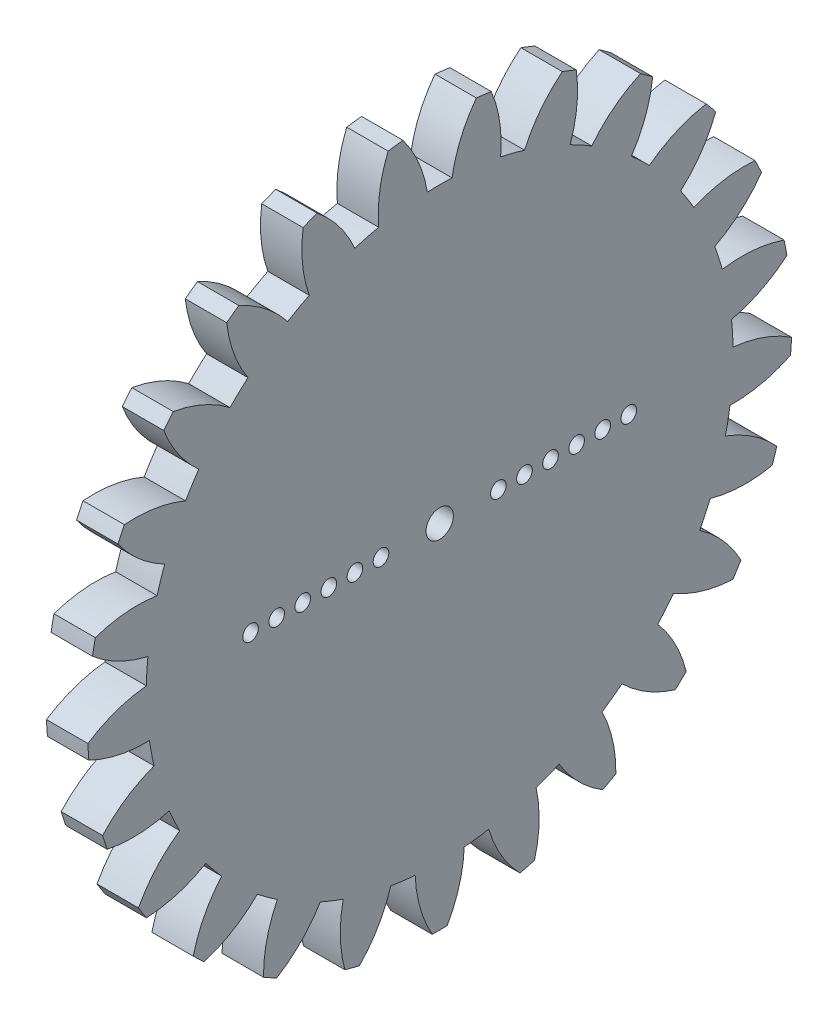
SolidWorks part; units mm, degrees
ref_plane "Plane1" through (0, 0, 0) normal (0, 0, 1) x (1, 0, 0)
ref_plane "Plane2" through (0, 0, 0) normal (0, 1, 0) x (1, 0, 0)
ref_plane "Plane3" through (0, 0, 0) normal (1, 0, 0) x (0, 0, -1)
sketch "HoldingSke" plane through (0, 0, 0) normal (0, 1, 0) x (1, 0, 0)
  line L0 (0, 0) -> (0.4532, -0.2113)
  line L1 (-15, 0) -> (100, 0) construction
  line L2 (0, 0) -> (-2.1039, 2.3779)
  line L3 (0, 0) -> (-11.863, 4.5341)
  line L4 (0, 0) -> (7.8269, 3.6497)
  line L5 (0, 0) -> (-46.8476, -17.4728)
  line L6 (0, 0) -> (-8.2896, -5.593)
  line L7 (-2.1039, 2.3779) -> (8.6586, 51.2059)
  line L8 (-76.2, 54.61) -> (-74.4, 54.61)
  line L9 (-71.009, 38.7566) -> (-53.1078, 45.2721)
  line L10 (-76.2, 71.12) -> (104.1128, 71.12)
  line L11 (0, 0) -> (-10, 0)
  line L12 (-76.2, 101.6) -> (-76.133, 101.6)
  line L13 (24.9733, 27.94) -> (52.9518, 28.4284)
  line L14 (24.9733, 27.94) -> (24.9743, 27.94)
  line L15 (24.9733, 27.94) -> (100.4006, 29.5858)
  line L16 (-63.627, -2) -> (-12.827, -2)
  circle A0 centre (0, 0) radius 5
  circle A1 centre (0, 0) radius 22.499
  circle A2 centre (0, 0) radius 37.5
  circle A3 centre (0, 0) radius 5
  dimension "MHD" = 44.998
  dimension "Hub_dia" = 75
  dimension "Bore" = 10
  dimension "MBD" = 10
  dimension "Num_teeth" = 25
  dimension "Pitch" = 0.5
  dimension "Overall_len" = 50
  dimension "Show_teeth" = 25
  dimension "Thickness" = 10
  dimension "OAL" = 50.0001
  dimension "T_dim" = 1.8
  dimension "Ap" = 20
  dimension "H" = 19.05
  dimension "Pitch_radius" = 180.3128
  dimension "Width" = 10
  dimension "Backlash" = 0.067
  dimension "Addendum_fac" = 1
  dimension "Dedendum_fac" = 1.25
  dimension "Clearance_fac" = 0.25
  dimension "Dedendum_add" = 0.001
  dimension "Module" = 2
sketch "BasProSke" plane through (0, 0, 0) normal (0, 1, 0) x (1, 0, 0)
  line L0 (-10, 0) -> (60, 0) construction
  line L1 (0, 0) -> (0, 27)
  line L2 (0, 0) -> (10, 0)
  line L3 (10, 0) -> (10, 27)
  line L4 (10, 27) -> (0, 27)
  dimension "Thickness" = 10
  dimension "Diameter" = 54
revolve "Base-Revolve" add sketch "BasProSke" angle 360 about L0
sketch "TooCutSke" plane through (0, 0, 0) normal (1, 0, 0) x (0, 0, -1)
  line L1 (0, 0) -> (0, 107) construction
  line L2 (0, 0) -> (-1.687, 24.943) construction
  line L3 (0, 0) -> (-6.2561, 49.5219) construction
  line L4 (-1.687, 24.943) -> (-3.128, 24.761) construction
  arc A0 (0.9462, 22.4791) -> (-0.9462, 22.4791) centre (0, 0) ccw
  arc A1 (2.8295, 26.8769) -> (-2.8295, 26.8769) centre (0, 0) ccw
  circle A2 centre (0, 0) radius 25 construction
  circle A3 centre (0, 0) radius 23.4923 construction
  arc A4 (-0.9462, 22.4791) -> (-2.8295, 26.8769) centre (-10.8135, 20.8556) ccw
  arc A5 (2.8295, 26.8769) -> (0.9462, 22.4791) centre (10.8135, 20.8556) ccw
  dimension "Root_dia" = 44.998
  dimension "Overcut_dia" = 54.0508
  dimension "Pitch_dia" = 50
  dimension "Base_dia" = 46.9846
  dimension "Flank_rad" = 10
  dimension "Half_ang" = 7.2
  dimension "Half_CT" = 1.4525
extrude "ToothCut" cut sketch "TooCutSke" along normal through all
fillet "Breaks" [suppressed] radius 0.04
fillet "RootFillets" [suppressed] radius 0.501
pattern_circular "TeethCuts" count 25 over 360 about axis through (0, 0, 0) along (1, 0, 0) of "ToothCut", "RootFillets", "Breaks"
sketch "HubNeaOneSke" plane through (0, 0, 0) normal (-1, 0, 0) x (0, 0, 1)
  circle A0 centre (0, 0) radius 22.499
  dimension "Diameter" = 44.998
extrude "HubNearOne" [suppressed] add sketch "HubNeaOneSke" along normal blind 40.0001
sketch "HubNeaBotSke" plane through (0, 0, 0) normal (-1, 0, 0) x (0, 0, 1)
  circle A0 centre (0, 0) radius 22.499
  dimension "Diameter" = 44.998
extrude "HubNearBoth" [suppressed] add sketch "HubNeaBotSke" along normal blind 20
ref_plane "FarPln" through (10, 0, 0) normal (1, 0, 0) x (0, 0, -1)
sketch "HubFarSke" plane through (10, 0, 0) normal (1, 0, 0) x (0, 0, -1)
  circle A0 centre (0, 0) radius 22.499
  dimension "Diameter" = 44.998
extrude "HubFar" [suppressed] add sketch "HubFarSke" along normal blind 20
sketch "BorSke" plane through (0, 0, 0) normal (1, 0, 0) x (0, 0, -1)
  circle A0 centre (0, 0) radius 5
  dimension "Diameter" = 10
extrude "Bore" [suppressed] cut sketch "BorSke" along normal mid plane 100.0001
sketch "KeySke" plane through (0, 0, 0) normal (1, 0, 0) x (0, 0, -1)
  line L0 (-2, 0) -> (-2, 6.8)
  line L1 (-2, 6.8) -> (2, 6.8)
  line L2 (2, 6.8) -> (2, 0)
  line L3 (0, 0) -> (0, 34) construction
  line L4 (-2, 0) -> (2, 0)
  dimension "Offset" = 6.8
  dimension "Width" = 4
extrude "Keyway" [suppressed] cut sketch "KeySke" along normal mid plane 100.0001
pattern_circular "Keyway2" [suppressed] count 2 every 90 about axis through (-10, 0, 0) along (1, 0, 0)
sketch "Sketch1" plane through (10, 0, 0) normal (1, 0, 0) x (0, 0, -1)
  arc A100 (-26.6237, 4.4923) -> (-22.3753, 2.3558) centre (-20.1355, 12.1017) ccw
  arc A101 (-26.6237, 4.4923) -> (-22.3753, 2.3558) centre (-20.1355, 12.1017) ccw
  arc A102 (-22.3753, 2.3558) -> (-22.4941, 0.4672) centre (0, 0) ccw
  arc A103 (-26.9768, -1.12) -> (-26.9044, -2.2699) centre (0, 0) ccw
  arc A104 (-22.3753, 2.3558) -> (-22.4941, 0.4672) centre (0, 0) ccw
  arc A105 (-22.4941, 0.4672) -> (-26.9768, -1.12) centre (-21.4935, -9.4826) ccw
  arc A106 (-22.4941, 0.4672) -> (-26.9768, -1.12) centre (-21.4935, -9.4826) ccw
  arc A107 (-26.9044, -2.2699) -> (-22.2582, -3.2828) centre (-22.5125, 6.714) ccw
  arc A108 (-26.9044, -2.2699) -> (-22.2582, -3.2828) centre (-22.5125, 6.714) ccw
  arc A109 (-22.2582, -3.2828) -> (-21.9036, -5.1416) centre (0, 0) ccw
  arc A110 (-22.2582, -3.2828) -> (-21.9036, -5.1416) centre (0, 0) ccw
  arc A111 (-21.9036, -5.1416) -> (-25.8507, -7.7937) centre (-18.46, -14.5299) ccw
  arc A112 (-21.9036, -5.1416) -> (-25.8507, -7.7937) centre (-18.46, -14.5299) ccw
  arc A113 (-25.8507, -7.7937) -> (-25.4947, -8.8895) centre (0, 0) ccw
  arc A114 (-25.8507, -7.7937) -> (-25.4947, -8.8895) centre (0, 0) ccw
  arc A115 (-25.4947, -8.8895) -> (-20.7425, -8.715) centre (-23.4749, 0.9044) ccw
  arc A116 (-25.4947, -8.8895) -> (-20.7425, -8.715) centre (-23.4749, 0.9044) ccw
  arc A117 (-20.7425, -8.715) -> (-19.9368, -10.4272) centre (0, 0) ccw
  arc A118 (-20.7425, -8.715) -> (-19.9368, -10.4272) centre (0, 0) ccw
  arc A119 (-19.9368, -10.4272) -> (-23.1004, -13.9776) centre (-14.2666, -18.6642) ccw
  arc A120 (-19.9368, -10.4272) -> (-23.1004, -13.9776) centre (-14.2666, -18.6642) ccw
  arc A121 (-23.1004, -13.9776) -> (-22.483, -14.9504) centre (0, 0) ccw
  arc A122 (-23.1004, -13.9776) -> (-22.483, -14.9504) centre (0, 0) ccw
  arc A123 (-22.483, -14.9504) -> (-17.9235, -13.5997) centre (-22.9623, -4.9619) ccw
  arc A124 (-22.483, -14.9504) -> (-17.9235, -13.5997) centre (-22.9623, -4.9619) ccw
  arc A125 (-17.9235, -13.5997) -> (-16.7173, -15.0577) centre (0, 0) ccw
  arc A126 (-17.9235, -13.5997) -> (-16.7173, -15.0577) centre (0, 0) ccw
  arc A127 (-16.7173, -15.0577) -> (-18.8985, -19.2833) centre (-9.1768, -21.6258) ccw
  arc A128 (-16.7173, -15.0577) -> (-18.8985, -19.2833) centre (-9.1768, -21.6258) ccw
  arc A129 (-18.8985, -19.2833) -> (-18.0586, -20.072) centre (0, 0) ccw
  arc A130 (-18.8985, -19.2833) -> (-18.0586, -20.072) centre (0, 0) ccw
  arc A131 (-18.0586, -20.072) -> (-13.9783, -17.6298) centre (-21.0069, -10.5165) ccw
  arc A132 (-18.0586, -20.072) -> (-13.9783, -17.6298) centre (-21.0069, -10.5165) ccw
  arc A133 (-13.9783, -17.6298) -> (-12.4474, -18.7421) centre (0, 0) ccw
  arc A134 (-13.9783, -17.6298) -> (-12.4474, -18.7421) centre (0, 0) ccw
  arc A135 (-12.4474, -18.7421) -> (-13.5092, -23.3774) centre (-3.5103, -23.2286) ccw
  arc A136 (-12.4474, -18.7421) -> (-13.5092, -23.3774) centre (-3.5103, -23.2286) ccw
  arc A137 (-13.5092, -23.3774) -> (-12.4996, -23.9324) centre (0, 0) ccw
  arc A138 (-13.5092, -23.3774) -> (-12.4996, -23.9324) centre (0, 0) ccw
  arc A139 (-12.4996, -23.9324) -> (-9.1548, -20.5522) centre (-17.7316, -15.4104) ccw
  arc A140 (-12.4996, -23.9324) -> (-9.1548, -20.5522) centre (-17.7316, -15.4104) ccw
  arc A141 (-9.1548, -20.5522) -> (-7.3954, -21.2488) centre (0, 0) ccw
  arc A142 (-9.1548, -20.5522) -> (-7.3954, -21.2488) centre (0, 0) ccw
  arc A143 (-7.3954, -21.2488) -> (-7.2711, -26.0025) centre (2.3767, -23.3718) ccw
  arc A144 (-7.3954, -21.2488) -> (-7.2711, -26.0025) centre (2.3767, -23.3718) ccw
  arc A145 (-7.2711, -26.0025) -> (-6.1551, -26.2891) centre (0, 0) ccw
  arc A146 (-7.2711, -26.0025) -> (-6.1551, -26.2891) centre (0, 0) ccw
  arc A147 (-6.1551, -26.2891) -> (-3.7561, -22.1833) centre (-13.3421, -19.3359) ccw
  arc A148 (-6.1551, -26.2891) -> (-3.7561, -22.1833) centre (-13.3421, -19.3359) ccw
  arc A149 (-3.7561, -22.1833) -> (-1.8787, -22.4204) centre (0, 0) ccw
  arc A150 (-3.7561, -22.1833) -> (-1.8787, -22.4204) centre (0, 0) ccw
  arc A151 (-1.8787, -22.4204) -> (-0.5761, -26.9939) centre (8.1143, -22.0465) ccw
  arc A152 (-1.8787, -22.4204) -> (-0.5761, -26.9939) centre (8.1143, -22.0465) ccw
  arc A153 (-0.5761, -26.9939) -> (0.5761, -26.9939) centre (0, 0) ccw
  arc A154 (-0.5761, -26.9939) -> (0.5761, -26.9939) centre (0, 0) ccw
  arc A155 (0.5761, -26.9939) -> (1.8787, -22.4204) centre (-8.1143, -22.0465) ccw
  arc A156 (0.5761, -26.9939) -> (1.8787, -22.4204) centre (-8.1143, -22.0465) ccw
  arc A157 (1.8787, -22.4204) -> (3.7561, -22.1833) centre (0, 0) ccw
  arc A158 (1.8787, -22.4204) -> (3.7561, -22.1833) centre (0, 0) ccw
  arc A159 (3.7561, -22.1833) -> (6.1551, -26.2891) centre (13.3421, -19.3359) ccw
  arc A160 (3.7561, -22.1833) -> (6.1551, -26.2891) centre (13.3421, -19.3359) ccw
  arc A161 (6.1551, -26.2891) -> (7.2711, -26.0025) centre (0, 0) ccw
  arc A162 (6.1551, -26.2891) -> (7.2711, -26.0025) centre (0, 0) ccw
  arc A163 (7.2711, -26.0025) -> (7.3954, -21.2488) centre (-2.3767, -23.3718) ccw
  arc A164 (7.2711, -26.0025) -> (7.3954, -21.2488) centre (-2.3767, -23.3718) ccw
  arc A165 (7.3954, -21.2488) -> (9.1548, -20.5522) centre (0, 0) ccw
  arc A166 (7.3954, -21.2488) -> (9.1548, -20.5522) centre (0, 0) ccw
  arc A167 (9.1548, -20.5522) -> (12.4996, -23.9324) centre (17.7316, -15.4104) ccw
  arc A168 (9.1548, -20.5522) -> (12.4996, -23.9324) centre (17.7316, -15.4104) ccw
  arc A169 (12.4996, -23.9324) -> (13.5092, -23.3774) centre (0, 0) ccw
  arc A170 (12.4996, -23.9324) -> (13.5092, -23.3774) centre (0, 0) ccw
  arc A171 (13.5092, -23.3774) -> (12.4474, -18.7421) centre (3.5103, -23.2286) ccw
  arc A172 (13.5092, -23.3774) -> (12.4474, -18.7421) centre (3.5103, -23.2286) ccw
  arc A173 (12.4474, -18.7421) -> (13.9783, -17.6298) centre (0, 0) ccw
  arc A174 (12.4474, -18.7421) -> (13.9783, -17.6298) centre (0, 0) ccw
  arc A175 (13.9783, -17.6298) -> (18.0586, -20.072) centre (21.0069, -10.5165) ccw
  arc A176 (2.8117, 26.8532) -> (0.9462, 22.4791) centre (10.8135, 20.8556) ccw
  arc A177 (0.9462, 22.4791) -> (-0.9462, 22.4791) centre (0, 0) ccw
  arc A178 (-0.9462, 22.4791) -> (-2.8117, 26.8532) centre (-10.8135, 20.8556) ccw
  arc A179 (13.9783, -17.6298) -> (18.0586, -20.072) centre (21.0069, -10.5165) ccw
  arc A180 (18.0586, -20.072) -> (18.8985, -19.2833) centre (0, 0) ccw
  arc A181 (18.0586, -20.072) -> (18.8985, -19.2833) centre (0, 0) ccw
  arc A182 (18.8985, -19.2833) -> (16.7173, -15.0577) centre (9.1768, -21.6258) ccw
  arc A183 (18.8985, -19.2833) -> (16.7173, -15.0577) centre (9.1768, -21.6258) ccw
  arc A184 (16.7173, -15.0577) -> (17.9235, -13.5997) centre (0, 0) ccw
  arc A185 (16.7173, -15.0577) -> (17.9235, -13.5997) centre (0, 0) ccw
  arc A186 (17.9235, -13.5997) -> (22.483, -14.9504) centre (22.9623, -4.9619) ccw
  arc A187 (17.9235, -13.5997) -> (22.483, -14.9504) centre (22.9623, -4.9619) ccw
  arc A188 (22.483, -14.9504) -> (23.1004, -13.9776) centre (0, 0) ccw
  arc A189 (22.483, -14.9504) -> (23.1004, -13.9776) centre (0, 0) ccw
  arc A190 (23.1004, -13.9776) -> (19.9368, -10.4272) centre (14.2666, -18.6642) ccw
  arc A191 (23.1004, -13.9776) -> (19.9368, -10.4272) centre (14.2666, -18.6642) ccw
  arc A192 (19.9368, -10.4272) -> (20.7425, -8.715) centre (0, 0) ccw
  arc A193 (19.9368, -10.4272) -> (20.7425, -8.715) centre (0, 0) ccw
  arc A194 (20.7425, -8.715) -> (25.4947, -8.8895) centre (23.4749, 0.9044) ccw
  arc A195 (20.7425, -8.715) -> (25.4947, -8.8895) centre (23.4749, 0.9044) ccw
  arc A196 (25.4947, -8.8895) -> (25.8507, -7.7937) centre (0, 0) ccw
  arc A197 (25.4947, -8.8895) -> (25.8507, -7.7937) centre (0, 0) ccw
  arc A198 (25.8507, -7.7937) -> (21.9036, -5.1416) centre (18.46, -14.5299) ccw
  arc A199 (25.8507, -7.7937) -> (21.9036, -5.1416) centre (18.46, -14.5299) ccw
  arc A203 (-26.9768, -1.12) -> (-26.9044, -2.2699) centre (0, 0) ccw
  arc A276 (2.8117, 26.8532) -> (0.9462, 22.4791) centre (10.8135, 20.8556) ccw
  arc A277 (0.9462, 22.4791) -> (-0.9462, 22.4791) centre (0, 0) ccw
  arc A278 (-0.9462, 22.4791) -> (-2.8117, 26.8532) centre (-10.8135, 20.8556) ccw
  arc A300 (21.9036, -5.1416) -> (22.2582, -3.2828) centre (0, 0) ccw
  arc A301 (21.9036, -5.1416) -> (22.2582, -3.2828) centre (0, 0) ccw
  arc A302 (22.2582, -3.2828) -> (26.9044, -2.2699) centre (22.5125, 6.714) ccw
  arc A303 (22.2582, -3.2828) -> (26.9044, -2.2699) centre (22.5125, 6.714) ccw
  arc A304 (26.9044, -2.2699) -> (26.9768, -1.12) centre (0, 0) ccw
  arc A305 (26.9044, -2.2699) -> (26.9768, -1.12) centre (0, 0) ccw
  arc A306 (26.9768, -1.12) -> (22.4941, 0.4672) centre (21.4935, -9.4826) ccw
  arc A307 (26.9768, -1.12) -> (22.4941, 0.4672) centre (21.4935, -9.4826) ccw
  arc A308 (22.4941, 0.4672) -> (22.3753, 2.3558) centre (0, 0) ccw
  arc A309 (22.4941, 0.4672) -> (22.3753, 2.3558) centre (0, 0) ccw
  arc A310 (22.3753, 2.3558) -> (26.6237, 4.4923) centre (20.1355, 12.1017) ccw
  arc A311 (22.3753, 2.3558) -> (26.6237, 4.4923) centre (20.1355, 12.1017) ccw
  arc A312 (26.6237, 4.4923) -> (26.4078, 5.624) centre (0, 0) ccw
  arc A313 (26.6237, 4.4923) -> (26.4078, 5.624) centre (0, 0) ccw
  arc A314 (26.4078, 5.624) -> (21.6713, 6.0466) centre (23.1764, -3.8395) ccw
  arc A315 (26.4078, 5.624) -> (21.6713, 6.0466) centre (23.1764, -3.8395) ccw
  arc A316 (21.6713, 6.0466) -> (21.0865, 7.8463) centre (0, 0) ccw
  arc A317 (21.6713, 6.0466) -> (21.0865, 7.8463) centre (0, 0) ccw
  arc A318 (21.0865, 7.8463) -> (24.6701, 10.9722) centre (16.4933, 16.729) ccw
  arc A319 (21.0865, 7.8463) -> (24.6701, 10.9722) centre (16.4933, 16.729) ccw
  arc A320 (24.6701, 10.9722) -> (24.1795, 12.0147) centre (0, 0) ccw
  arc A321 (24.6701, 10.9722) -> (24.1795, 12.0147) centre (0, 0) ccw
  arc A322 (24.1795, 12.0147) -> (19.4867, 11.246) centre (23.4031, 2.0449) ccw
  arc A323 (24.1795, 12.0147) -> (19.4867, 11.246) centre (23.4031, 2.0449) ccw
  arc A324 (19.4867, 11.246) -> (18.4728, 12.8438) centre (0, 0) ccw
  arc A325 (19.4867, 11.246) -> (18.4728, 12.8438) centre (0, 0) ccw
  arc A326 (18.4728, 12.8438) -> (21.1663, 16.7626) centre (11.8148, 20.3051) ccw
  arc A327 (18.4728, 12.8438) -> (21.1663, 16.7626) centre (11.8148, 20.3051) ccw
  arc A328 (21.1663, 16.7626) -> (20.4319, 17.6504) centre (0, 0) ccw
  arc A329 (21.1663, 16.7626) -> (20.4319, 17.6504) centre (0, 0) ccw
  arc A330 (20.4319, 17.6504) -> (16.0777, 15.7389) centre (22.1594, 7.8008) ccw
  arc A331 (20.4319, 17.6504) -> (16.0777, 15.7389) centre (22.1594, 7.8008) ccw
  arc A332 (16.0777, 15.7389) -> (14.6983, 17.0342) centre (0, 0) ccw
  arc A333 (16.0777, 15.7389) -> (14.6983, 17.0342) centre (0, 0) ccw
  arc A334 (14.6983, 17.0342) -> (16.3327, 21.4999) centre (6.394, 22.6054) ccw
  arc A335 (14.6983, 17.0342) -> (16.3327, 21.4999) centre (6.394, 22.6054) ccw
  arc A336 (16.3327, 21.4999) -> (15.4005, 22.1771) centre (0, 0) ccw
  arc A337 (16.3327, 21.4999) -> (15.4005, 22.1771) centre (0, 0) ccw
  arc A338 (15.4005, 22.1771) -> (11.6585, 19.2428) centre (19.5232, 13.0665) ccw
  arc A339 (15.4005, 22.1771) -> (11.6585, 19.2428) centre (19.5232, 13.0665) ccw
  arc A340 (11.6585, 19.2428) -> (10.0003, 20.1544) centre (0, 0) ccw
  arc A341 (11.6585, 19.2428) -> (10.0003, 20.1544) centre (0, 0) ccw
  arc A342 (10.0003, 20.1544) -> (10.4727, 24.8862) centre (0.5713, 23.4854) ccw
  arc A343 (10.0003, 20.1544) -> (10.4727, 24.8862) centre (0.5713, 23.4854) ccw
  arc A344 (10.4727, 24.8862) -> (9.4015, 25.3103) centre (0, 0) ccw
  arc A345 (10.4727, 24.8862) -> (9.4015, 25.3103) centre (0, 0) ccw
  arc A346 (9.4015, 25.3103) -> (6.5068, 21.5376) centre (15.6604, 17.5112) ccw
  arc A347 (9.4015, 25.3103) -> (6.5068, 21.5376) centre (15.6604, 17.5112) ccw
  arc A348 (6.5068, 21.5376) -> (4.6739, 22.0082) centre (0, 0) ccw
  arc A349 (6.5068, 21.5376) -> (4.6739, 22.0082) centre (0, 0) ccw
  arc A350 (4.6739, 22.0082) -> (3.9548, 26.7088) centre (-5.2872, 22.8896) ccw
  arc A351 (4.6739, 22.0082) -> (3.9548, 26.7088) centre (-5.2872, 22.8896) ccw
  arc A352 (3.9548, 26.7088) -> (2.8117, 26.8532) centre (0, 0) ccw
  arc A353 (3.9548, 26.7088) -> (2.8117, 26.8532) centre (0, 0) ccw
  arc A354 (-2.8117, 26.8532) -> (-3.9548, 26.7088) centre (0, 0) ccw
  arc A355 (-2.8117, 26.8532) -> (-3.9548, 26.7088) centre (0, 0) ccw
  arc A356 (-3.9548, 26.7088) -> (-4.6739, 22.0082) centre (5.2872, 22.8896) ccw
  arc A357 (-3.9548, 26.7088) -> (-4.6739, 22.0082) centre (5.2872, 22.8896) ccw
  arc A358 (-4.6739, 22.0082) -> (-6.5068, 21.5376) centre (0, 0) ccw
  arc A359 (-4.6739, 22.0082) -> (-6.5068, 21.5376) centre (0, 0) ccw
  arc A360 (-6.5068, 21.5376) -> (-9.4015, 25.3103) centre (-15.6604, 17.5112) ccw
  arc A361 (-6.5068, 21.5376) -> (-9.4015, 25.3103) centre (-15.6604, 17.5112) ccw
  arc A362 (-9.4015, 25.3103) -> (-10.4727, 24.8862) centre (0, 0) ccw
  arc A363 (-9.4015, 25.3103) -> (-10.4727, 24.8862) centre (0, 0) ccw
  arc A364 (-10.4727, 24.8862) -> (-10.0003, 20.1544) centre (-0.5713, 23.4854) ccw
  arc A365 (-10.4727, 24.8862) -> (-10.0003, 20.1544) centre (-0.5713, 23.4854) ccw
  arc A366 (-10.0003, 20.1544) -> (-11.6585, 19.2428) centre (0, 0) ccw
  arc A367 (-10.0003, 20.1544) -> (-11.6585, 19.2428) centre (0, 0) ccw
  arc A368 (-11.6585, 19.2428) -> (-15.4005, 22.1771) centre (-19.5232, 13.0665) ccw
  arc A369 (-11.6585, 19.2428) -> (-15.4005, 22.1771) centre (-19.5232, 13.0665) ccw
  arc A370 (-15.4005, 22.1771) -> (-16.3327, 21.4999) centre (0, 0) ccw
  arc A371 (-15.4005, 22.1771) -> (-16.3327, 21.4999) centre (0, 0) ccw
  arc A372 (-16.3327, 21.4999) -> (-14.6983, 17.0342) centre (-6.394, 22.6054) ccw
  arc A373 (-16.3327, 21.4999) -> (-14.6983, 17.0342) centre (-6.394, 22.6054) ccw
  arc A374 (-14.6983, 17.0342) -> (-16.0777, 15.7389) centre (0, 0) ccw
  arc A375 (-14.6983, 17.0342) -> (-16.0777, 15.7389) centre (0, 0) ccw
  arc A376 (-16.0777, 15.7389) -> (-20.4319, 17.6504) centre (-22.1594, 7.8008) ccw
  arc A377 (-16.0777, 15.7389) -> (-20.4319, 17.6504) centre (-22.1594, 7.8008) ccw
  arc A378 (-20.4319, 17.6504) -> (-21.1663, 16.7626) centre (0, 0) ccw
  arc A379 (-20.4319, 17.6504) -> (-21.1663, 16.7626) centre (0, 0) ccw
  arc A380 (-21.1663, 16.7626) -> (-18.4728, 12.8438) centre (-11.8148, 20.3051) ccw
  arc A381 (-21.1663, 16.7626) -> (-18.4728, 12.8438) centre (-11.8148, 20.3051) ccw
  arc A382 (-18.4728, 12.8438) -> (-19.4867, 11.246) centre (0, 0) ccw
  arc A383 (-18.4728, 12.8438) -> (-19.4867, 11.246) centre (0, 0) ccw
  arc A384 (-19.4867, 11.246) -> (-24.1795, 12.0147) centre (-23.4031, 2.0449) ccw
  arc A385 (-19.4867, 11.246) -> (-24.1795, 12.0147) centre (-23.4031, 2.0449) ccw
  arc A386 (-24.1795, 12.0147) -> (-24.6701, 10.9722) centre (0, 0) ccw
  arc A387 (-24.1795, 12.0147) -> (-24.6701, 10.9722) centre (0, 0) ccw
  arc A388 (-24.6701, 10.9722) -> (-21.0865, 7.8463) centre (-16.4933, 16.729) ccw
  arc A389 (-24.6701, 10.9722) -> (-21.0865, 7.8463) centre (-16.4933, 16.729) ccw
  arc A390 (-21.0865, 7.8463) -> (-21.6713, 6.0466) centre (0, 0) ccw
  arc A391 (-21.0865, 7.8463) -> (-21.6713, 6.0466) centre (0, 0) ccw
  arc A392 (-21.6713, 6.0466) -> (-26.4078, 5.624) centre (-23.1764, -3.8395) ccw
  arc A393 (-21.6713, 6.0466) -> (-26.4078, 5.624) centre (-23.1764, -3.8395) ccw
  arc A394 (-26.4078, 5.624) -> (-26.6237, 4.4923) centre (0, 0) ccw
  arc A395 (-26.4078, 5.624) -> (-26.6237, 4.4923) centre (0, 0) ccw
  dimension "D1" = 0
extrude "Cut-Extrude1" cut sketch "Sketch1" against normal blind 6.825
sketch "Sketch2" plane through (0, 0, 0) normal (-1, 0, 0) x (0, 0, 1)
  line L0 (0, -50) -> (0, 50) construction
  circle A0 centre (0, 0) radius 1.05
  circle A1 centre (4.5, 0) radius 0.6
  circle A2 centre (6.5, 0) radius 0.6
  circle A3 centre (8.5, 0) radius 0.6
  circle A4 centre (10.5, 0) radius 0.6
  circle A5 centre (12.5, 0) radius 0.6
  circle A6 centre (14.5, 0) radius 0.6
  circle A7 centre (-14.5, 0) radius 0.6
  circle A8 centre (-12.5, 0) radius 0.6
  circle A9 centre (-10.5, 0) radius 0.6
  circle A10 centre (-8.5, 0) radius 0.6
  circle A11 centre (-6.5, 0) radius 0.6
  circle A12 centre (-4.5, 0) radius 0.6
  dimension "D1" = 2.1
  dimension "D2" = 4.5
  dimension "D3" = 1.2
  dimension "D4" = 6
extrude "Cut-Extrude2" cut sketch "Sketch2" against normal through all
equation "' \"Module@HoldingSke\" = 6.35"
equation "' \"Num_teeth@HoldingSke\" = 12"
equation "' \"Ap@HoldingSke\" =  20"
equation "' \"Ap@HoldingSke\" = 20"
equation "' \"Width@HoldingSke\" = 0.5 * 25.4"
equation "' \"Hub_dia@HoldingSke\"= 1 * 25.4"
equation "' \"Hub_dia@HoldingSke\" = 1 * 25.4"
equation "' \"Overall_len@HoldingSke\" = 1.0 * 25.4"
equation "' \"Bore@HoldingSke\" = 0.75 * 25.4"
equation "' \"T_dim@HoldingSke\" = 0.1 * 25.4"
equation "' \"Width@KeySke\" = 0.25 * 25.4"
equation "' \"Show_teeth@HoldingSke\" = 13"
equation "' \"Backlash@HoldingSke\" = 0.009 * 25.4"
equation "' \"Addendum_fac@HoldingSke\" = 1.0"
equation "' \"Dedendum_fac@HoldingSke\" = 1.25"
equation "' \"Dedendum_add@HoldingSke\" = 0.00005 * 25.4"
equation "' \"Clearance_fac@HoldingSke\" = 0.25"
equation "\"Pitch@HoldingSke\" = 1 / \"Module@HoldingSke\""
equation "\"Overcut_dia@TooCutSke\" = (\"Num_teeth@HoldingSke\" + 2 * \"Addendum_fac@HoldingSke\") / \"Pitch@HoldingSke\" + 0.002 * 25.4"
equation "\"Pitch_dia@TooCutSke\" = \"Num_teeth@HoldingSke\" / \"Pitch@HoldingSke\""
equation "\"Base_dia@TooCutSke\" = \"Num_teeth@HoldingSke\" / \"Pitch@HoldingSke\" * cos((\"Ap@HoldingSke\"  * 3.14159265 / 180))"
equation "\"Root_dia@TooCutSke\" = (\"Num_teeth@HoldingSke\" + 2) / \"Pitch@HoldingSke\" - 2 * (\"Addendum_fac@HoldingSke\" + \"Dedendum_fac@HoldingSke\") / \"Pitch@HoldingSke\" - \"Dedendum_add@HoldingSke\" * 2"
equation "\"Half_ang@TooCutSke\" = 180 / \"Num_teeth@HoldingSke\""
equation "\"Half_CT@TooCutSke\" = \"Num_teeth@HoldingSke\" / \"Pitch@HoldingSke\" * sin((3.14159265 / 2 / \"Num_teeth@HoldingSke\")) / 2 - 7 * \"Backlash@HoldingSke\" / 4"
equation "\"Flank_rad@TooCutSke\" = \"Num_teeth@HoldingSke\" / \"Pitch@HoldingSke\" / 5"
equation "\"Radius@RootFillets\" = \"Clearance_fac@HoldingSke\" / \"Pitch@HoldingSke\" + \"Dedendum_add@HoldingSke\""
equation "\"Break_rad@Breaks\" = 0.02 / \"Pitch@HoldingSke\""
equation "\"Thickness@HoldingSke\" = \"Width@HoldingSke\""
equation "\"OAL@HoldingSke\" = \"Thickness@HoldingSke\""
equation "\"MHD@HoldingSke\" = (\"Num_teeth@HoldingSke\" + 2) / \"Pitch@HoldingSke\" - 2 * (\"Addendum_fac@HoldingSke\" + \"Dedendum_fac@HoldingSke\")  / \"Pitch@HoldingSke\" - \"Dedendum_add@HoldingSke\" * 2"
equation "\"MBD@HoldingSke\" = (\"Num_teeth@HoldingSke\" + 2) / \"Pitch@HoldingSke\" - 2 * (\"Addendum_fac@HoldingSke\" + \"Dedendum_fac@HoldingSke\")  / \"Pitch@HoldingSke\" - \"Dedendum_add@HoldingSke\" * 2 - 0.002 * 25.4"
equation "\"MHD@HoldingSke\" = ((sgn( \"MHD@HoldingSke\" - \"Hub_dia@HoldingSke\" )-1)*( \"MHD@HoldingSke\" - \"Hub_dia@HoldingSke\" ))/-2+ \"Hub_dia@HoldingSke\""
equation "\"MBD@HoldingSke\" = ((sgn( \"MBD@HoldingSke\" - \"Bore@HoldingSke\" )-1)*( \"MBD@HoldingSke\" - \"Bore@HoldingSke\" ))/-2+ \"Bore@HoldingSke\""
equation "\"OAL@HoldingSke\" = ((sgn( \"OAL@HoldingSke\" - \"Overall_len@HoldingSke\" )+1)*( \"OAL@HoldingSke\" - \"Overall_len@HoldingSke\" ))/2 + \"Overall_len@HoldingSke\" + 0.000002 * 25.4"
equation "\"Num_teeth@TeethCuts\" = int( \"Show_teeth@HoldingSke\" ) + 1"
equation "\"Num_teeth@TeethCuts\" = ((sgn( \"Num_teeth@TeethCuts\" - \"Num_teeth@HoldingSke\" )-1)*( \"Num_teeth@TeethCuts\" - \"Num_teeth@HoldingSke\" ))/-2+ \"Num_teeth@HoldingSke\""
equation "\"Num_teeth@TeethCuts\" = ((sgn( \"Num_teeth@TeethCuts\" - 2.0)+1)*( \"Num_teeth@TeethCuts\" - 2.0))/2 +2.0"
equation "\"Angle@TeethCuts\" = 360.0 / \"Num_teeth@HoldingSke\""
equation "\"Diameter@BasProSke\" = (\"Num_teeth@HoldingSke\" + 2 * \"Addendum_fac@HoldingSke\") / \"Pitch@HoldingSke\""
equation "\"Thickness@BasProSke\"  = \"Thickness@HoldingSke\""
equation "' \"Fillet_rad@BasProSke\" =  \"Thickness@HoldingSke\" * 0.05"
equation "' \"Fillet_rad@BasProSke\" = \"Thickness@HoldingSke\" * 0.05"
equation "\"MHD@HoldingSke\" = ((sgn( \"MHD@HoldingSke\" - \"Root_dia@TooCutSke\" )-1)*( \"MHD@HoldingSke\" - \"Root_dia@TooCutSke\" ))/-2+ \"Root_dia@TooCutSke\""
equation "\"Diameter@HubNeaOneSke\" = \"MHD@HoldingSke\""
equation "\"Length@HubNearOne\" = \"OAL@HoldingSke\" - \"Thickness@BasProSke\""
equation "\"Diameter@HubNeaBotSke\" = \"MHD@HoldingSke\""
equation "\"Length@HubNearBoth\" = ( \"OAL@HoldingSke\" - \"Thickness@BasProSke\" ) / 2.0"
equation "\"Thickness@FarPln\" = \"Thickness@BasProSke\""
equation "\"Diameter@HubFarSke\" = \"MHD@HoldingSke\""
equation "\"Length@HubFar\" = ( \"OAL@HoldingSke\" - \"Thickness@BasProSke\" ) / 2.0"
equation "\"Diameter@BorSke\" = \"MBD@HoldingSke\""
equation "\"D1@Bore\" = \"OAL@HoldingSke\" * 2.0"
equation "\"D1@Keyway\" = \"OAL@HoldingSke\" * 2.0"
equation "\"Offset@KeySke\" = \"T_dim@HoldingSke\" + \"MBD@HoldingSke\" / 2.0"
